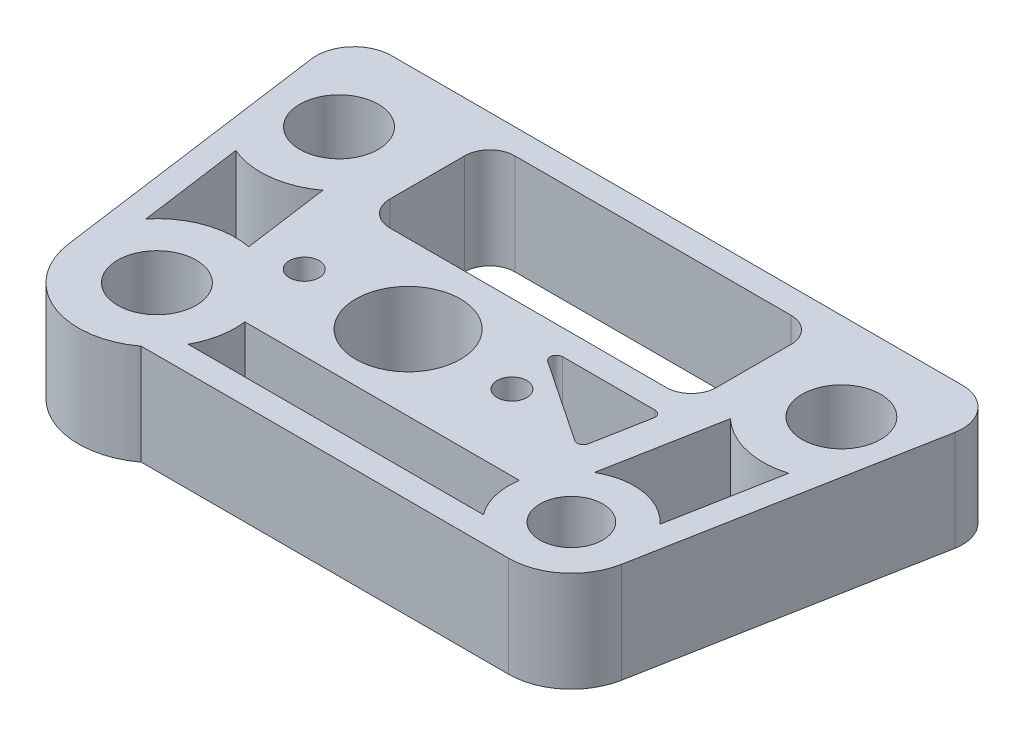
SolidWorks part; units mm, degrees
material "7075-T6 (SN)"
ref_plane "X-Y Datum" through (0, 0, 0) normal (0, 0, 1) x (1, 0, 0)
ref_plane "X-Z Datum" through (0, 0, 0) normal (0, 1, 0) x (1, 0, 0)
ref_plane "Y-Z Datum" through (0, 0, 0) normal (1, 0, 0) x (0, 0, -1)
sketch "Sketch1" plane through (0, 0, 0) normal (0, 1, 0) x (1, 0, 0)
  line L1 (54.2925, 13.97) -> (-12.3825, 13.97) construction
  line L4 (54.2925, 31.75) -> (-12.3825, 31.75)
  line L6 (46.355, 22.86) -> (-4.445, 22.86) construction
  line L7 (54.2925, 31.75) -> (54.2925, 13.97)
  line L8 (-12.3825, 31.75) -> (-12.3825, 13.97)
  line L21 (-7.9375, 0) -> (-12.3825, 13.97)
  line L22 (6.264, 8.509) -> (16.764, 8.509) construction
  line L24 (16.764, 8.509) -> (27.264, 8.509) construction
  line L25 (7.0861, -3.5764) -> (36.6629, -3.5764)
  line L27 (48.26, 0) -> (54.2925, 13.97)
  circle A0 centre (0, 0) radius 3.9688
  circle A1 centre (41.91, 0) radius 3.175
  circle A2 centre (46.355, 22.86) radius 3.9688
  circle A3 centre (-4.445, 22.86) radius 3.9687
  arc A5 (7.0861, -3.5764) -> (-7.9375, 0) centre (0, 0) cw
  circle A7 centre (16.764, 8.509) radius 5.3
  circle A8 centre (6.264, 8.509) radius 1.5
  circle A9 centre (27.264, 8.509) radius 1.5
  arc A10 (36.6629, -3.5764) -> (48.26, 0) centre (41.91, 0) ccw
  dimension "D2" = 6.35
  dimension "D7" = 7.9375
  dimension "D8" = 6.35
  dimension "D12" = 10.6
  dimension "D10" = 7.9375
  dimension "D17" = 3
  dimension "D19" = 7.9375
  dimension "D18" = 7.9375
  dimension "D3" = 50.8
  dimension "D4" = 17.78
  dimension "D5" = 8.89
  dimension "D6" = 31.75
  dimension "D9" = 4.445
  dimension "D11" = 7.9375
  dimension "D13" = 16.764
  dimension "D14" = 5.461
  dimension "D16" = 10.5
  dimension "D20" = 41.91
extrude "Boss-Extrude1" [suppressed] add sketch "Sketch1" against normal blind 10.16
sketch "Sketch3" [suppressed] plane through (0, 0, 0) normal (0, 1, 0) x (1, 0, 0)
  line L0 (0, 0) -> (0, -44.5462) construction
  line L1 (0, 0) -> (26.3151, -45.579) construction
  dimension "D1" = 30
other "Graphic1"
other "Graphic (Closed) -1"
other "Graphic2"
other "Graphic (Closed) -2"
sketch "Sketch4" plane through (0, 0, 0) normal (0, 1, 0) x (1, 0, 0)
  line L0 (34.925, 29.21) -> (6.985, 29.21)
  line L1 (54.2925, 31.75) -> (-12.3825, 31.75)
  line L5 (27.264, 8.636) -> (16.764, 8.636) construction
  line L6 (16.764, 8.636) -> (6.264, 8.636) construction
  line L7 (46.355, 22.86) -> (-4.445, 22.86) construction
  line L8 (-4.445, 22.86) -> (-12.3825, 22.86) construction
  line L9 (54.2925, 13.97) -> (-12.3825, 13.97) construction
  line L17 (-12.3825, 31.75) -> (-7.8634, -1.0823)
  line L19 (48.1523, -1.1645) -> (54.2925, 31.75)
  line L25 (4.445, 26.67) -> (4.445, 19.1135)
  line L27 (37.465, 19.1135) -> (37.465, 26.67)
  line L28 (46.587, 4.2951) -> (48.6317, 15.256)
  line L29 (38.7374, 5.5007) -> (40.9001, 17.0939)
  line L30 (36.83, -3.81) -> (6.9633, -3.81)
  line L31 (35.6418, 1.016) -> (7.8722, 1.016)
  line L32 (-6.1407, 5.0295) -> (-7.5919, 15.573)
  line L33 (1.4909, 7.7962) -> (0.2939, 16.4924)
  line L35 (34.925, 16.5735) -> (6.985, 16.5735)
  line L36 (35.9215, 7.7189) -> (36.9593, 13.282)
  line L37 (36.3351, 14.0335) -> (27.0034, 14.0335)
  line L38 (34.9435, 7.308) -> (26.6497, 12.8711)
  line L39 (41.91, -6.35) -> (4.7625, -6.35)
  circle A0 centre (0, 0) radius 3.9688
  circle A1 centre (46.355, 22.86) radius 3.9687
  circle A2 centre (-4.445, 22.86) radius 3.9688
  circle A3 centre (16.764, 8.636) radius 5.2959
  circle A4 centre (27.264, 8.636) radius 1.5
  circle A5 centre (6.264, 8.636) radius 1.5
  circle A6 centre (41.91, 0) radius 3.175
  arc A15 (-7.8634, -1.0823) -> (4.7625, -6.35) centre (0, 0) ccw
  arc A16 (41.91, -6.35) -> (48.1523, -1.1645) centre (41.91, 0) ccw
  arc A17 (34.925, 29.21) -> (37.465, 26.67) centre (34.925, 26.67) cw
  arc A18 (4.445, 26.67) -> (6.985, 29.21) centre (6.985, 26.67) cw
  arc A21 (46.587, 4.2951) -> (38.7374, 5.5007) centre (41.91, 0) ccw
  arc A22 (48.6317, 15.256) -> (40.9001, 17.0939) centre (46.355, 22.86) cw
  arc A23 (36.83, -3.81) -> (35.6418, 1.016) centre (41.91, 0) cw
  arc A24 (6.9633, -3.81) -> (7.8722, 1.016) centre (0, 0) ccw
  arc A25 (-6.1407, 5.0295) -> (1.4909, 7.7962) centre (0, 0) cw
  arc A26 (-7.5919, 15.573) -> (0.2939, 16.4924) centre (-4.445, 22.86) ccw
  arc A27 (4.445, 19.1135) -> (6.985, 16.5735) centre (6.985, 19.1135) ccw
  arc A28 (34.925, 16.5735) -> (37.465, 19.1135) centre (34.925, 19.1135) ccw
  arc A29 (26.6497, 12.8711) -> (27.0034, 14.0335) centre (27.0034, 13.3985) cw
  arc A30 (36.3351, 14.0335) -> (36.9593, 13.282) centre (36.3351, 13.3985) cw
  arc A31 (34.9435, 7.308) -> (35.9215, 7.7189) centre (35.2972, 7.8353) ccw
  point P28 (37.465, 29.21)
  point P33 (4.445, 29.21)
  point P66 (35.7446, 6.7707)
  dimension "D1" = 7.9375
  dimension "D2" = 7.9375
  dimension "D3" = 6.35
  dimension "D4" = 10.5918
  dimension "D5" = 3
  dimension "D27" = 7.9375
  dimension "D28" = 7.62
  dimension "D29" = 6.35
  dimension "D30" = 7.9375
  dimension "D35" = 7.9375
  dimension "D36" = 2.54
  dimension "D37" = 2.54
  dimension "D22" = 2.54
  dimension "D24" = 7.9375
  dimension "D25" = 6.35
  dimension "D26" = 6.35
  dimension "D33" = 7.9375
  dimension "D34" = 7.9375
  dimension "D40" = 0.635
  dimension "D6" = 10.5
  dimension "D7" = 22.86
  dimension "D8" = 50.8
  dimension "D9" = 7.9375
  dimension "D10" = 4.445
  dimension "D11" = 8.636
  dimension "D12" = 16.764
  dimension "D13" = 41.91
  dimension "D14" = 17.78
  dimension "D15" = 8.89
  dimension "D16" = 7.9375
  dimension "D17" = 3.175
  dimension "D18" = 2.54
  dimension "D19" = 8.89
  dimension "D20" = 2.54
  dimension "D21" = 7.9375
  dimension "D23" = 2.54
  dimension "D31" = 8.89
  dimension "D32" = 7.9375
  dimension "D38" = 3.175
  dimension "D39" = 1.27
extrude "Boss-Extrude2" add sketch "Sketch4" along normal blind 10.16
ref_point "Point1"
ref_point "Point2"
sketch "Sketch5" plane through (0, 10.16, 0) normal (0, 1, 0) x (1, 0, 0)
  line L0 (0, 0) -> (0, -25.3617) construction
  line L1 (0, 0) -> (11.466, -19.8596) construction
  dimension "D1" = 30
fillet "Fillet1" radius 3.81 2 edges at (-12.3825, 5.08, -31.75) (54.2925, 5.08, -31.75)
